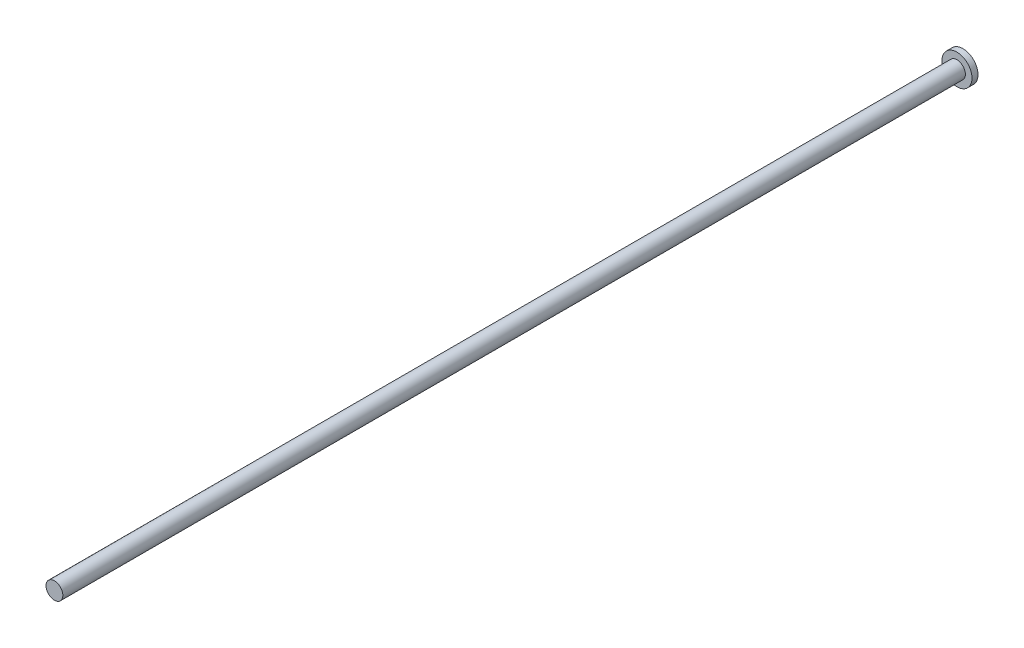
SolidWorks part; units mm, degrees
ref_plane "Front Plane" through (0, 0, 0) normal (0, 0, 1) x (1, 0, 0)
ref_plane "Top Plane" through (0, 0, 0) normal (0, 1, 0) x (1, 0, 0)
ref_plane "Right Plane" through (0, 0, 0) normal (1, 0, 0) x (0, 0, -1)
sketch "Sketch2" plane through (0, 0, 0) normal (0, 0, 1) x (1, 0, 0)
  circle A0 centre (0, 0) radius 2.5
  dimension "D1" = 5
extrude "Boss-Extrude1" add sketch "Sketch2" along normal blind 1
sketch "Sketch3" plane through (0, 0, 1) normal (0, 0, 1) x (1, 0, 0)
  circle A0 centre (0, 0) radius 1.4
  dimension "D1" = 2.8
extrude "Boss-Extrude2" add sketch "Sketch3" along normal blind 150
